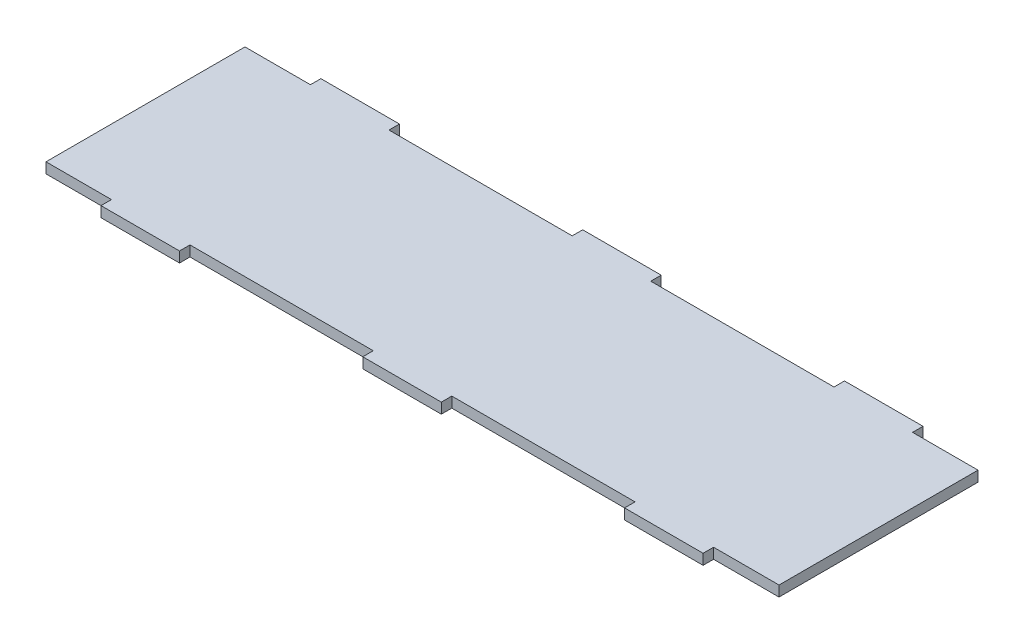
SolidWorks part; units mm, degrees
material "Acrílico (médio-alto impacto)"
ref_plane "Plano frontal" through (0, 0, 0) normal (0, 0, 1) x (1, 0, 0)
ref_plane "Plano superior" through (0, 0, 0) normal (0, 1, 0) x (1, 0, 0)
ref_plane "Plano direito" through (0, 0, 0) normal (1, 0, 0) x (0, 0, -1)
sketch "Esboço1" plane through (0, 0, 0) normal (0, 1, 0) x (1, 0, 0)
  line L0 (15, 0) -> (-15, 0)
  line L1 (-15, 0) -> (-15, 4)
  line L2 (-15, 4) -> (-85, 4)
  line L3 (-85, 4) -> (-85, 0)
  line L4 (-85, 0) -> (-115, 0)
  line L5 (-115, 0) -> (-115, 4)
  line L6 (-115, 4) -> (-140, 4)
  line L27 (-140, 80) -> (-140, 4)
  line L28 (-155.8537, 42) -> (204.1463, 42) construction
  line L29 (0, 0) -> (0, 115.2392) construction
  line L30 (140, 80) -> (140, 4)
  line L31 (115, 4) -> (140, 4)
  line L32 (115, 0) -> (115, 4)
  line L33 (85, 0) -> (115, 0)
  line L34 (85, 4) -> (85, 0)
  line L35 (15, 4) -> (85, 4)
  line L36 (15, 0) -> (15, 4)
  line L37 (15, 84) -> (15, 80)
  line L38 (15, 80) -> (85, 80)
  line L39 (85, 80) -> (85, 84)
  line L40 (85, 84) -> (115, 84)
  line L41 (115, 84) -> (115, 80)
  line L42 (115, 80) -> (140, 80)
  line L43 (-115, 80) -> (-140, 80)
  line L44 (-115, 84) -> (-115, 80)
  line L45 (-85, 84) -> (-115, 84)
  line L46 (-85, 80) -> (-85, 84)
  line L47 (-15, 80) -> (-85, 80)
  line L48 (-15, 84) -> (-15, 80)
  line L49 (15, 84) -> (-15, 84)
  point P24 (0, 0)
  point P36 (140, 42)
  point P37 (-140, 42)
  point P43 (0, 84)
  dimension "D1" = 4
  dimension "D2" = 30
  dimension "D3" = 15
  dimension "D4" = 4
  dimension "D5" = 4
  dimension "D6" = 38
  dimension "D8" = 25
  dimension "D9" = 70
extrude "Ressalto-extrusão1" add sketch "Esboço1" along normal blind 4
